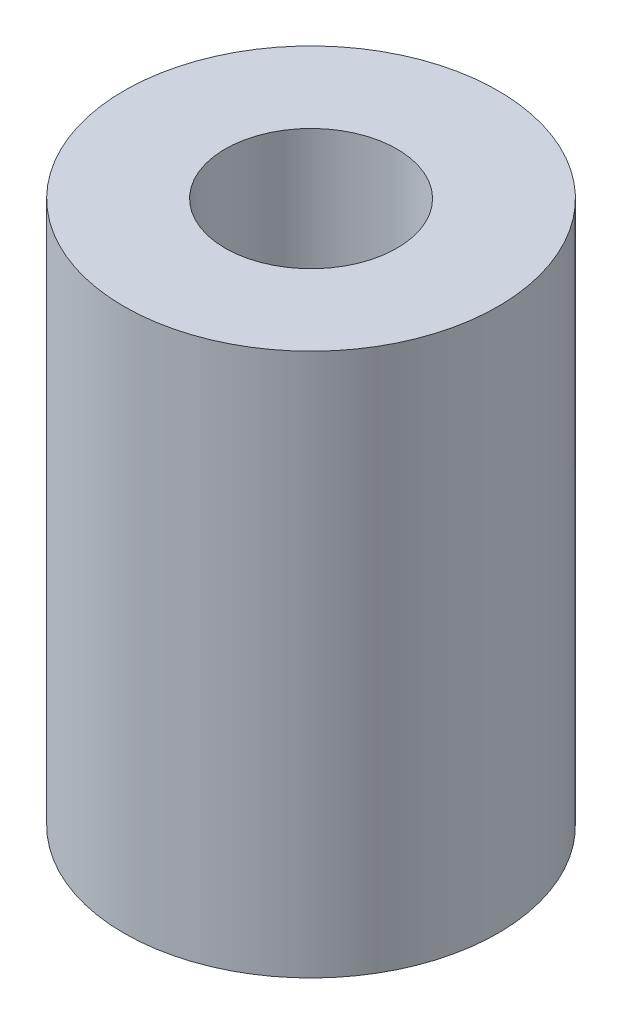
SolidWorks part; units mm, degrees
ref_plane "Front Plane" through (0, 0, 0) normal (0, 0, 1) x (1, 0, 0)
ref_plane "Top Plane" through (0, 0, 0) normal (0, 1, 0) x (1, 0, 0)
ref_plane "Right Plane" through (0, 0, 0) normal (1, 0, 0) x (0, 0, -1)
sketch "Sketch1" plane through (0, 0, 0) normal (0, 1, 0) x (1, 0, 0)
  circle A0 centre (0, 0) radius 3.1
  dimension "D1" = 6.2
extrude "Boss-Extrude1" add sketch "Sketch1" along normal blind 9
sketch "Sketch2" plane through (0, 9, 0) normal (0, 1, 0) x (1, 0, 0)
  circle A0 centre (0, 0) radius 1.425
  dimension "D1" = 2.85
extrude "Cut-Extrude1" cut sketch "Sketch2" against normal through all
